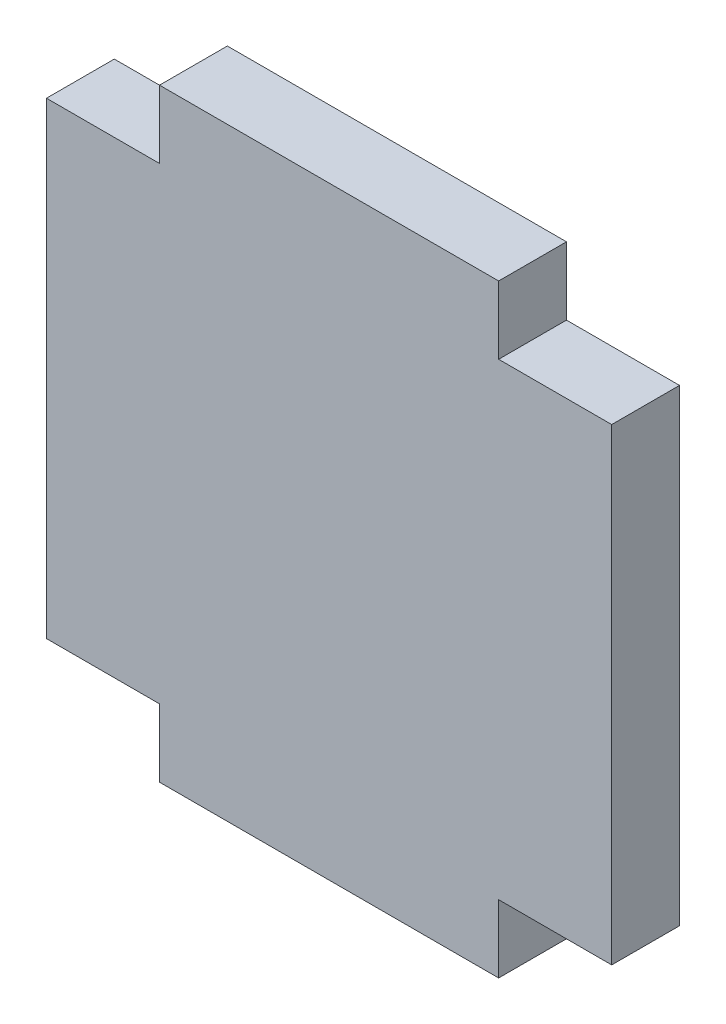
SolidWorks part; units mm, degrees
material "MDF"
ref_plane "Plano frontal" through (0, 0, 0) normal (0, 0, 1) x (1, 0, 0)
ref_plane "Plano superior" through (0, 0, 0) normal (0, 1, 0) x (1, 0, 0)
ref_plane "Plano direito" through (0, 0, 0) normal (1, 0, 0) x (0, 0, -1)
sketch "Esboço1" plane through (0, 0, 0) normal (0, 0, 1) x (1, 0, 0)
  line L0 (12.5, 0) -> (0, 0) construction
  line L1 (-12.5, -10.35) -> (12.5, -10.35)
  line L2 (-12.5, -10.35) -> (-12.5, 10.35)
  line L3 (-12.5, 10.35) -> (12.5, 10.35)
  line L4 (12.5, -10.35) -> (12.5, 10.35)
  line L5 (-12.5, -10.35) -> (12.5, 10.35) construction
  line L6 (-12.5, 10.35) -> (12.5, -10.35) construction
  line L7 (7.5, 13.35) -> (-7.5, 13.35)
  line L8 (7.5, 13.35) -> (7.5, 10.35)
  line L9 (7.5, 10.35) -> (-7.5, 10.35)
  line L10 (-7.5, 13.35) -> (-7.5, 10.35)
  line L11 (7.5, 13.35) -> (-7.5, 10.35) construction
  line L12 (7.5, 10.35) -> (-7.5, 13.35) construction
  line L13 (7.5, -10.35) -> (-7.5, -10.35)
  line L14 (-7.5, -13.35) -> (-7.5, -10.35)
  line L15 (7.5, -13.35) -> (-7.5, -13.35)
  line L16 (7.5, -13.35) -> (7.5, -10.35)
  point P0 (0, 0)
  point P6 (0, 11.85)
  dimension "D1" = 3
  dimension "D2" = 15
  dimension "D3" = 5
  dimension "D4" = 20.7
extrude "Ressalto-extrusão1" add sketch "Esboço1" along normal blind 3 contours L1 L4 L3 L2 | L7 L10 L3 L8 | L15 L16 L1 L14
